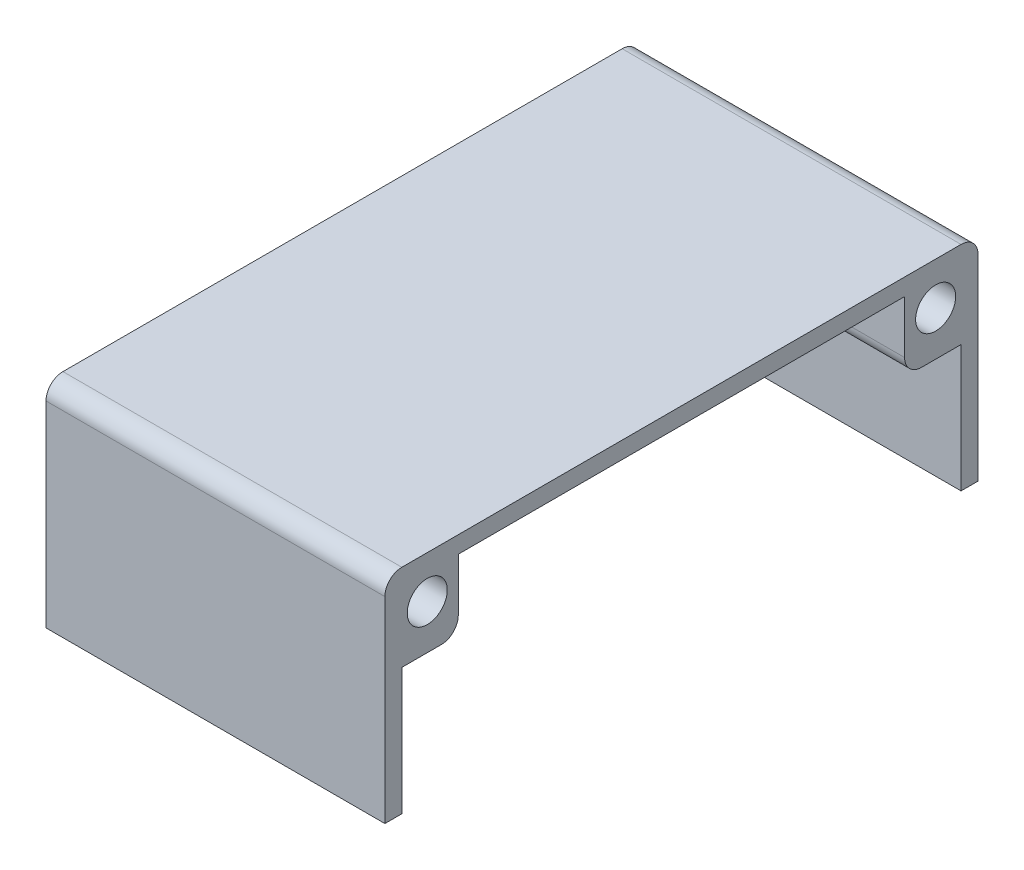
SolidWorks part; units mm, degrees
ref_plane "Front Plane" through (0, 0, 0) normal (0, 0, 1) x (1, 0, 0)
ref_plane "Top Plane" through (0, 0, 0) normal (0, 1, 0) x (1, 0, 0)
ref_plane "Right Plane" through (0, 0, 0) normal (1, 0, 0) x (0, 0, -1)
sketch "Sketch1" plane through (0, 0, 0) normal (1, 0, 0) x (0, 0, -1)
  line L1 (-44.4525, -16.002) -> (44.4525, -16.002)
  line L2 (-44.4525, -16.002) -> (-44.4525, 16.002)
  line L3 (-44.4525, 16.002) -> (44.4525, 16.002)
  line L4 (44.4525, -16.002) -> (44.4525, 16.002)
  line L5 (-44.4525, -16.002) -> (44.4525, 16.002) construction
  line L6 (-44.4525, 16.002) -> (44.4525, -16.002) construction
  point P0 (0, 0)
  dimension "D1" = 88.905
  dimension "D2" = 32.004
extrude "Boss-Extrude1" add sketch "Sketch1" along normal blind 50.8
fillet "Fillet1" radius 2.54 1 edges at (25.4, 16.002, -44.4525)
fillet "Fillet2" radius 2.54 1 edges at (25.4, 16.002, 44.4525)
sketch "Sketch13" plane through (0, 0, 0) normal (-1, 0, 0) x (0, 0, 1)
  line L0 (-44.4525, -16.002) -> (-44.4525, 13.462) construction
  line L1 (-41.9125, -16.002) -> (41.9125, -16.002)
  line L2 (-41.9125, -16.002) -> (-41.9125, 13.462)
  line L3 (-41.9125, 13.462) -> (41.9125, 13.462)
  line L4 (41.9125, -16.002) -> (41.9125, 13.462)
  line L5 (44.4525, 13.462) -> (44.4525, -16.002) construction
  line L6 (44.4525, -16.002) -> (-44.4525, -16.002) construction
  dimension "D1" = 2.54
  dimension "D2" = 2.54
  dimension "D3" = 29.464
extrude "Cut-Extrude1" cut sketch "Sketch13" against normal blind 90
sketch "Sketch15" plane through (0, 0, 0) normal (-1, 0, 0) x (0, 0, 1)
  line L0 (44.4525, 13.462) -> (44.4525, -16.002) construction
  line L1 (-41.9125, 16.002) -> (41.9125, 16.002) construction
  line L2 (41.9125, 13.462) -> (-41.9125, 13.462) construction
  line L3 (33.4525, 13.462) -> (41.9125, 13.462)
  line L4 (33.4525, 13.462) -> (33.4525, 3.002)
  line L5 (33.4525, 3.002) -> (41.9125, 3.002)
  line L6 (41.9125, 13.462) -> (41.9125, 3.002)
  line L7 (41.9125, -16.002) -> (41.9125, 13.462) construction
  circle A0 centre (38.1025, 9.652) radius 3
  dimension "D1" = 6.35
  dimension "D2" = 6
  dimension "D3" = 6.35
  dimension "D4" = 13
  dimension "D5" = 11
sketch "Sketch19" plane through (0, 0, 0) normal (-1, 0, 0) x (0, 0, 1)
  line L3 (-41.9125, 16.002) -> (41.9125, 16.002) construction
  line L4 (-44.4525, -16.002) -> (-44.4525, 13.462) construction
  line L8 (-41.9125, 13.462) -> (-33.4525, 13.462)
  line L9 (-41.9125, 13.462) -> (-41.9125, 3.002)
  line L10 (-41.9125, 3.002) -> (-33.4525, 3.002)
  line L11 (-33.4525, 13.462) -> (-33.4525, 3.002)
  line L20 (33.4525, 3.002) -> (41.9125, 3.002) construction
  line L21 (33.4525, 13.462) -> (33.4525, 3.002) construction
  circle A0 centre (-38.1025, 9.652) radius 3
  dimension "D1" = 6.35
  dimension "D2" = 6
  dimension "D3" = 6.35
extrude "Boss-Extrude8" add sketch "Sketch15" against normal blind 50.8
extrude "Boss-Extrude9" add sketch "Sketch19" against normal blind 50.8
fillet "Fillet3" radius 2.54 2 edges at (25.4, 3.002, 33.4525) (25.4, 3.002, -33.4525)
